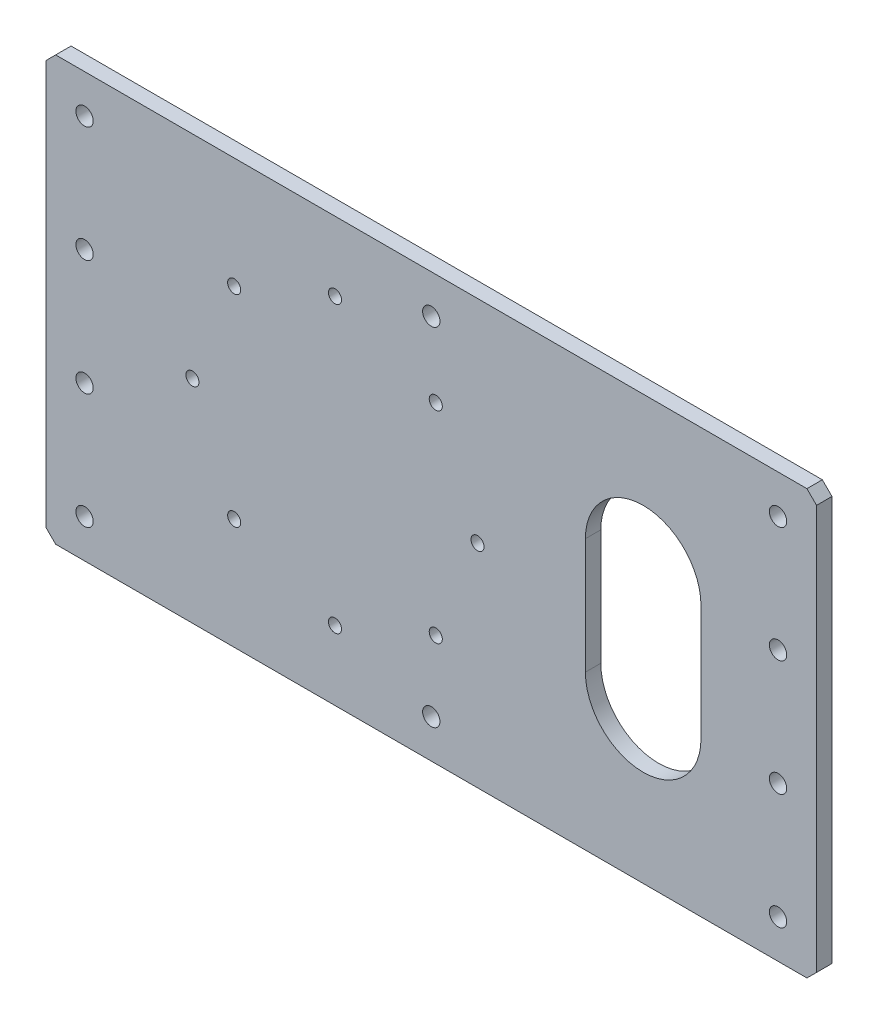
SolidWorks part; units mm, degrees
material "6061-T6 (SS)"
ref_plane "前视基准面" through (0, 0, 0) normal (0, 0, 1) x (1, 0, 0)
ref_plane "上视基准面" through (0, 0, 0) normal (0, 1, 0) x (1, 0, 0)
ref_plane "右视基准面" through (0, 0, 0) normal (1, 0, 0) x (0, 0, -1)
sketch "草图1" plane through (0, 0, 0) normal (0, 0, 1) x (1, 0, 0)
  line L1 (200, -110) -> (-200, -110)
  line L2 (200, -110) -> (200, 110)
  line L3 (200, 110) -> (-200, 110)
  line L4 (-200, -110) -> (-200, 110)
  line L5 (200, -110) -> (-200, 110) construction
  line L6 (200, 110) -> (-200, -110) construction
  point P0 (0, 0)
  dimension "D1" = 400
  dimension "D2" = 220
extrude "凸台-拉伸1" add sketch "草图1" along normal blind 8
sketch "草图3" plane through (0, 0, 8) normal (0, 0, 1) x (1, 0, 0)
  line L0 (200, 0) -> (-50, 0) construction
  line L1 (-50, 0) -> (-50, -110) construction
  line L2 (-102.3259, 52.3259) -> (2.3259, -52.3259) construction
  line L3 (-108.917, 44.7749) -> (-5.2251, -58.917) construction
  line L4 (0, 0) -> (0, 128.8251) construction
  line L5 (200, -110) -> (200, 110) construction
  line L6 (-200, -110) -> (200, -110) construction
  line L7 (-50, 0) -> (2.3259, 52.3259) construction
  circle A0 centre (-50, 0) radius 74 construction
  circle A1 centre (24, 0) radius 2.5
  circle A5 centre (-5.2251, -58.917) radius 3 construction
  circle A6 centre (-108.917, 44.7749) radius 3 construction
  circle A7 centre (-50, -74) radius 2.5
  circle A8 centre (-124, 0) radius 2.5
  circle A9 centre (-50, 74) radius 2.5
  circle A10 centre (2.3259, 52.3259) radius 2.3259
  circle A11 centre (2.3259, -52.3259) radius 2.3259
  circle A12 centre (-102.3259, -52.3259) radius 2.3259
  circle A13 centre (-102.3259, 52.3259) radius 2.3259
  point P16 (0, 0)
  point P25 (-50, 0)
  point P38 (-50, 0)
  dimension "D1" = 148
  dimension "D2" = 5
  dimension "D3" = 50
  dimension "D6" = 6
  dimension "D4" = 45
  dimension "D5" = 10
  dimension "D8" = 45
  dimension "D7" = 4
  dimension "D9" = 4
extrude "切除-拉伸1" cut sketch "草图3" against normal blind 10
sketch "草图4" plane through (0, 0, 0) normal (0, 0, -1) x (-1, 0, 0)
  line L0 (169.4178, 0) -> (-169.4178, 0) construction
  line L1 (0, 0) -> (0, 117.8091) construction
  line L2 (180, 110) -> (180, -110) construction
  line L3 (-200, 110) -> (200, 110) construction
  line L4 (200, -110) -> (-200, -110) construction
  line L5 (-180, 110) -> (-180, -110) construction
  line L6 (200, 110) -> (200, -110) construction
  circle A0 centre (180, 30) radius 4.5
  circle A1 centre (180, 90) radius 4.5
  circle A2 centre (180, -30) radius 4.5
  circle A4 centre (180, -90) radius 4.5
  circle A5 centre (-180, -90) radius 4.5
  circle A7 centre (-180, -30) radius 4.5
  circle A8 centre (-180, 90) radius 4.5
  circle A9 centre (-180, 30) radius 4.5
  dimension "D2" = 9
  dimension "D3" = 30
  dimension "D5" = 60
  dimension "D7" = 60
  dimension "D1" = 20
  dimension "D4" = 2
  dimension "D6" = 2
extrude "切除-拉伸2" cut sketch "草图4" against normal blind 10
sketch "草图5" plane through (0, 0, 0) normal (0, 0, -1) x (-1, 0, 0)
  line L0 (0, 0) -> (-200, 0) construction
  line L1 (-200, -110) -> (-200, 110) construction
  line L2 (-160, 110) -> (-160, -110) construction
  line L3 (-200, 110) -> (200, 110) construction
  line L4 (200, -110) -> (-200, -110) construction
  line L5 (-110, 30) -> (-110, -30) construction
  line L6 (-80, 30) -> (-80, -30)
  line L7 (-140, 30) -> (-140, -30)
  circle A0 centre (-110, 0) radius 30 construction
  arc A1 (-80, 30) -> (-140, 30) centre (-110, 30) ccw
  arc A2 (-140, -30) -> (-80, -30) centre (-110, -30) ccw
  point P16 (-110, 0)
  dimension "D1" = 60
  dimension "D2" = 90
  dimension "D3" = 40
extrude "切除-拉伸3" cut sketch "草图5" against normal blind 10
hole_wizard "M8 螺纹孔1" positions "草图6" profile "草图7" tap size "M8" standard "GB" end condition up to next
sketch "草图6" plane through (0, 0, 0) normal (0, 0, -1) x (-1, 0, 0)
  point P0 (50, 74)
  point P3 (124, 0)
  point P6 (50, -74)
  point P9 (-24, 0)
sketch "草图7" plane through (-50, 74, 0) normal (1, 0, 0) x (0, 1, 0)
  line L0 (0, 0) -> (0, 8)
  line L1 (0, 8) -> (3.4, 8)
  line L2 (3.4, 8) -> (3.4, 0)
  line L5 (3.4, 0) -> (0, 0)
  line L11 (0, -6.35) -> (0, 107.95) construction
  dimension "通孔螺纹孔钻头直径" = 6.8
  dimension "通孔螺纹孔钻头深度" = 8
cosmetic thread "孔螺蚊线1" parameters "D2"=8
cosmetic thread "孔螺蚊线2" parameters "D2"=8
cosmetic thread "孔螺蚊线3" parameters "D2"=8
cosmetic thread "孔螺蚊线4" parameters "D2"=8
hole_wizard "M8 螺纹孔2" positions "草图8" profile "草图9" tap size "M8" standard "GB" end condition up to next
sketch "草图8" plane through (0, 0, 0) normal (0, 0, -1) x (-1, 0, 0)
  point P0 (-2.3259, 52.3259)
sketch "草图9" plane through (2.3259, 52.3259, 0) normal (1, 0, 0) x (0, 1, 0)
  line L0 (0, 0) -> (0, 8)
  line L1 (0, 8) -> (3.4, 8)
  line L2 (3.4, 8) -> (3.4, 0)
  line L5 (3.4, 0) -> (0, 0)
  line L11 (0, -6.35) -> (0, 107.95) construction
  dimension "通孔螺纹孔钻头直径" = 6.8
  dimension "通孔螺纹孔钻头深度" = 8
cosmetic thread "孔螺蚊线5" parameters "D2"=8
hole_wizard "M8 螺纹孔3" positions "草图10" profile "草图11" tap size "M8" standard "GB" end condition up to next
sketch "草图10" plane through (0, 0, 0) normal (0, 0, -1) x (-1, 0, 0)
  point P0 (102.3259, 52.3259)
  point P3 (102.3259, -52.3259)
  point P6 (-2.3259, -52.3259)
sketch "草图11" plane through (-102.3259, 52.3259, 0) normal (1, 0, 0) x (0, 1, 0)
  line L0 (0, 0) -> (0, 8)
  line L1 (0, 8) -> (3.4, 8)
  line L2 (3.4, 8) -> (3.4, 0)
  line L5 (3.4, 0) -> (0, 0)
  line L11 (0, -6.35) -> (0, 107.95) construction
  dimension "通孔螺纹孔钻头直径" = 6.8
  dimension "通孔螺纹孔钻头深度" = 8
cosmetic thread "孔螺蚊线6" parameters "D2"=8
cosmetic thread "孔螺蚊线7" parameters "D2"=8
cosmetic thread "孔螺蚊线8" parameters "D2"=8
chamfer "倒角1" distance 5 angle 45 4 edges at (-200, -110, 4) (-200, 110, 4) (200, -110, 4) (200, 110, 4)
sketch "草图12" plane through (0, 0, 0) normal (0, 0, -1) x (-1, 0, 0)
  line L0 (-180, 90) -> (180, 90) construction
  line L1 (-180, -90) -> (180, -90) construction
  circle A0 centre (0, 90) radius 4.5
  circle A1 centre (0, -90) radius 4.5
  dimension "D1" = 9
extrude "切除-拉伸4" cut sketch "草图12" against normal blind 10
